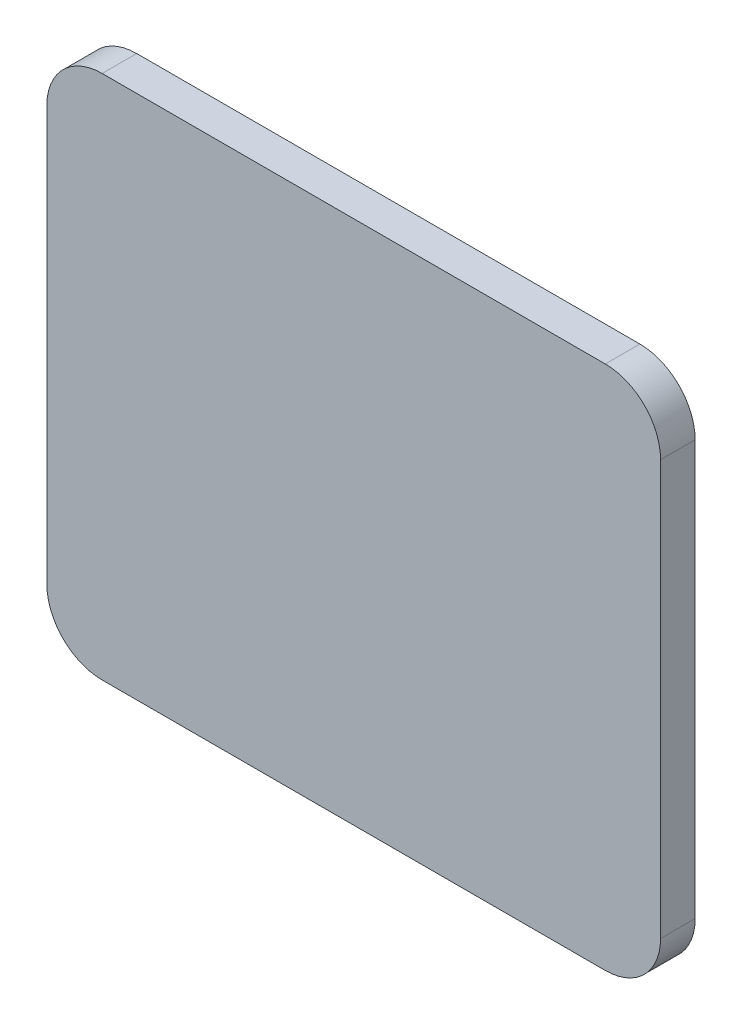
SolidWorks part; units mm, degrees
ref_plane "Plane1" through (0, 0, 0) normal (0, 0, 1) x (1, 0, 0)
ref_plane "Plane2" through (0, 0, 0) normal (0, 1, 0) x (1, 0, 0)
ref_plane "Plane3" through (0, 0, 0) normal (1, 0, 0) x (0, 0, -1)
sketch "Sketch1" plane through (0, 0, 0) normal (0, 0, 1) x (1, 0, 0)
  line L1 (11.557, -12.065) -> (-11.557, -12.065)
  line L2 (14.097, -9.525) -> (14.097, 9.525)
  line L3 (11.557, 12.065) -> (-11.557, 12.065)
  line L4 (-14.097, -9.525) -> (-14.097, 9.525)
  line L5 (14.097, -12.065) -> (-14.097, 12.065) construction
  line L6 (14.097, 12.065) -> (-14.097, -12.065) construction
  arc A0 (-11.557, -12.065) -> (-14.097, -9.525) centre (-11.557, -9.525) cw
  arc A1 (11.557, -12.065) -> (14.097, -9.525) centre (11.557, -9.525) ccw
  arc A2 (14.097, 9.525) -> (11.557, 12.065) centre (11.557, 9.525) ccw
  arc A3 (-11.557, 12.065) -> (-14.097, 9.525) centre (-11.557, 9.525) ccw
  point P0 (0, 0)
  dimension "D3" = 2.54
  dimension "D1" = 28.194
  dimension "D2" = 24.13
extrude "Boss-Extrude1" add sketch "Sketch1" along normal blind 1.5875
